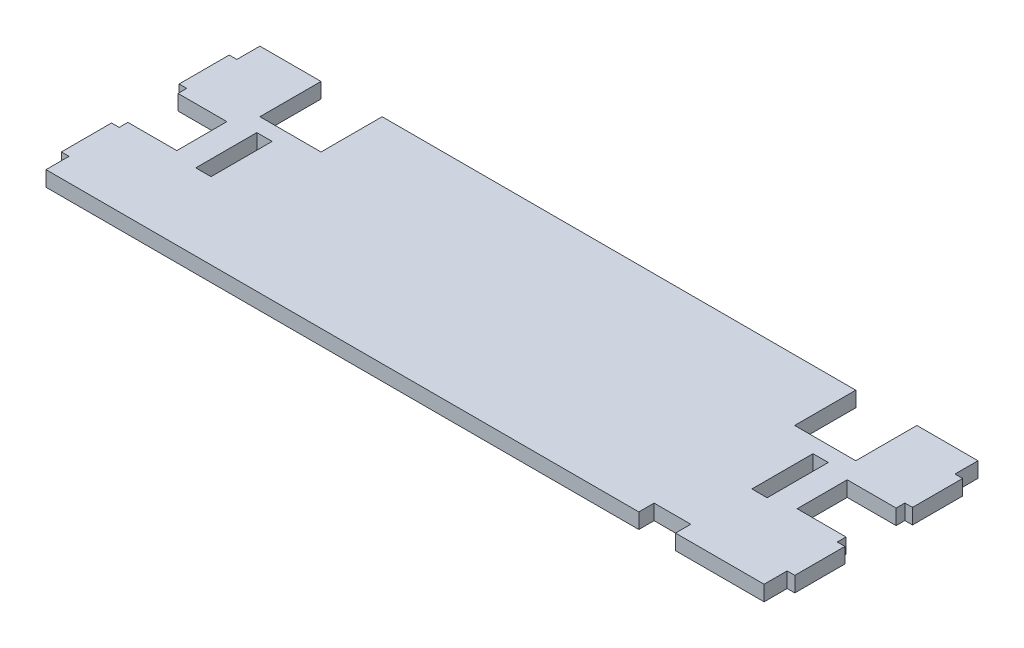
SolidWorks part; units mm, degrees
ref_plane "Front Plane" through (0, 0, 0) normal (0, 0, 1) x (1, 0, 0)
ref_plane "Top Plane" through (0, 0, 0) normal (0, 1, 0) x (1, 0, 0)
ref_plane "Right Plane" through (0, 0, 0) normal (1, 0, 0) x (0, 0, -1)
sketch "Sketch1" plane through (0, 0, 0) normal (0, 1, 0) x (1, 0, 0)
  line L0 (0, 72.39) -> (0, -44.45) construction
  line L1 (149.225, -44.45) -> (112.395, -44.45)
  line L2 (149.225, -44.45) -> (149.225, -34.8747)
  line L3 (149.225, 44.45) -> (123.825, 44.45)
  line L4 (-149.225, -44.45) -> (-149.225, -34.8747)
  line L5 (149.225, -44.45) -> (-149.225, 44.45) construction
  line L6 (149.225, 44.45) -> (-149.225, -44.45) construction
  line L7 (149.225, 10.414) -> (128.905, 10.414)
  line L9 (149.225, -10.414) -> (128.905, -10.414)
  line L10 (128.905, 10.414) -> (128.905, -10.414)
  line L11 (-123.825, 44.45) -> (-149.225, 44.45)
  line L13 (-149.225, -10.414) -> (-128.905, -10.414)
  line L14 (-128.905, 10.414) -> (-128.905, -10.414)
  line L15 (-149.225, 10.414) -> (-128.905, 10.414)
  line L17 (-127, 0) -> (127, 0) construction
  line L18 (-149.225, 14.0467) -> (-152.4, 14.0467)
  line L20 (-149.225, 34.8747) -> (-152.4, 34.8747)
  line L21 (-152.4, 14.0467) -> (-152.4, 34.8747)
  line L22 (-149.225, -34.8747) -> (-152.4, -34.8747)
  line L23 (-152.4, -14.0467) -> (-152.4, -34.8747)
  line L24 (-149.225, -14.0467) -> (-152.4, -14.0467)
  line L27 (149.225, -14.0467) -> (152.4, -14.0467)
  line L28 (152.4, -14.0467) -> (152.4, -34.8747)
  line L29 (149.225, -34.8747) -> (152.4, -34.8747)
  line L30 (149.225, 34.8747) -> (152.4, 34.8747)
  line L31 (152.4, 14.0467) -> (152.4, 34.8747)
  line L32 (149.225, 14.0467) -> (152.4, 14.0467)
  line L34 (-149.225, 34.8747) -> (-149.225, 44.45)
  line L35 (-149.225, -14.0467) -> (-149.225, -10.414)
  line L36 (149.225, 34.8747) -> (149.225, 44.45)
  line L37 (149.225, -14.0467) -> (149.225, -10.414)
  line L38 (-149.225, 10.414) -> (-149.225, 14.0467)
  line L39 (149.225, 10.414) -> (149.225, 14.0467)
  line L40 (-123.825, 44.45) -> (-123.825, 19.05)
  line L41 (-123.825, 19.05) -> (-98.425, 19.05)
  line L42 (-98.425, 44.45) -> (-98.425, 19.05)
  line L44 (98.425, 44.45) -> (98.425, 19.05)
  line L45 (98.425, 19.05) -> (123.825, 19.05)
  line L46 (123.825, 44.45) -> (123.825, 19.05)
  line L47 (98.425, 44.45) -> (-98.425, 44.45)
  line L48 (97.155, -44.45) -> (-149.225, -44.45)
  line L50 (97.155, -44.45) -> (97.155, -38.1)
  line L51 (97.155, -38.1) -> (112.395, -38.1)
  line L52 (112.395, -44.45) -> (112.395, -38.1)
  point P0 (0, 0)
  point P6 (127, 0)
  point P47 (104.775, -38.1)
  dimension "D1" = 298.45
  dimension "D2" = 88.9
  dimension "D3" = 20.828
  dimension "D5" = 3.175
  dimension "D6" = 20.828
  dimension "D4" = 20.32
  dimension "D7" = 25.4
  dimension "D8" = 25.4
  dimension "D9" = 25.4
  dimension "D10" = 25.4
  dimension "D12" = 25.4
  dimension "D11" = 25.4
  dimension "D13" = 304.8
  dimension "D14" = 15.24
  dimension "D15" = 6.35
  dimension "D16" = 47.625
extrude "Boss-Extrude1" add sketch "Sketch1" along normal mid plane 6.35
sketch "Sketch2" plane through (0, 0, 0) normal (0, 1, 0) x (1, 0, 0)
  line L1 (112.395, -12.7) -> (118.745, -12.7)
  line L2 (112.395, -12.7) -> (112.395, 12.7)
  line L3 (112.395, 12.7) -> (118.745, 12.7)
  line L4 (118.745, -12.7) -> (118.745, 12.7)
  line L5 (112.395, -12.7) -> (118.745, 12.7) construction
  line L6 (112.395, 12.7) -> (118.745, -12.7) construction
  line L13 (128.905, -10.414) -> (128.905, 10.414) construction
  line L15 (-112.395, -12.7) -> (-112.395, 12.7)
  line L16 (-112.395, -12.7) -> (-118.745, -12.7)
  line L17 (-118.745, -12.7) -> (-118.745, 12.7)
  line L18 (-112.395, 12.7) -> (-118.745, 12.7)
  point P0 (115.57, 0)
  point P10 (128.905, 0)
  dimension "D2" = 10.16
  dimension "D4" = 25.4
  dimension "D5" = 6.35
extrude "Cut-Extrude1" cut sketch "Sketch2" against normal through all both and the other way through all
equation "\"length\"= \"Avionics_Board_Length\""
equation "\"width\"=3.5"
equation "\"height\"= 0.25"
equation "\"D2@Sketch1\"=\"width\""
equation "\"eyebolt width\"= 0.82"
equation "\"eyebolt length\"= 0.8"
equation "\"D3@Sketch1\"=\"eyebolt width\""
equation "\"D4@Sketch1\"=\"eyebolt length\""
equation "\"lead screw holder height\"= 2.76"
equation "\"distance from holders to board\"=0.4"
equation "\"Mid_Coupler_Length\" = 12in"
equation "\"Avionics_Bulkhead_Thickness\" = 0.25in"
equation "\"Avionics_Bulkhead_Lip\" = 0.125in"
equation "\"Avionics_Board_Length\" = \"Mid_Coupler_Length\" - 2*\"Avionics_Bulkhead_Lip\""
equation "\"Body_Tube_OD\"= 4.024in"
equation "\"D1@Sketch1\"=\"length\""
